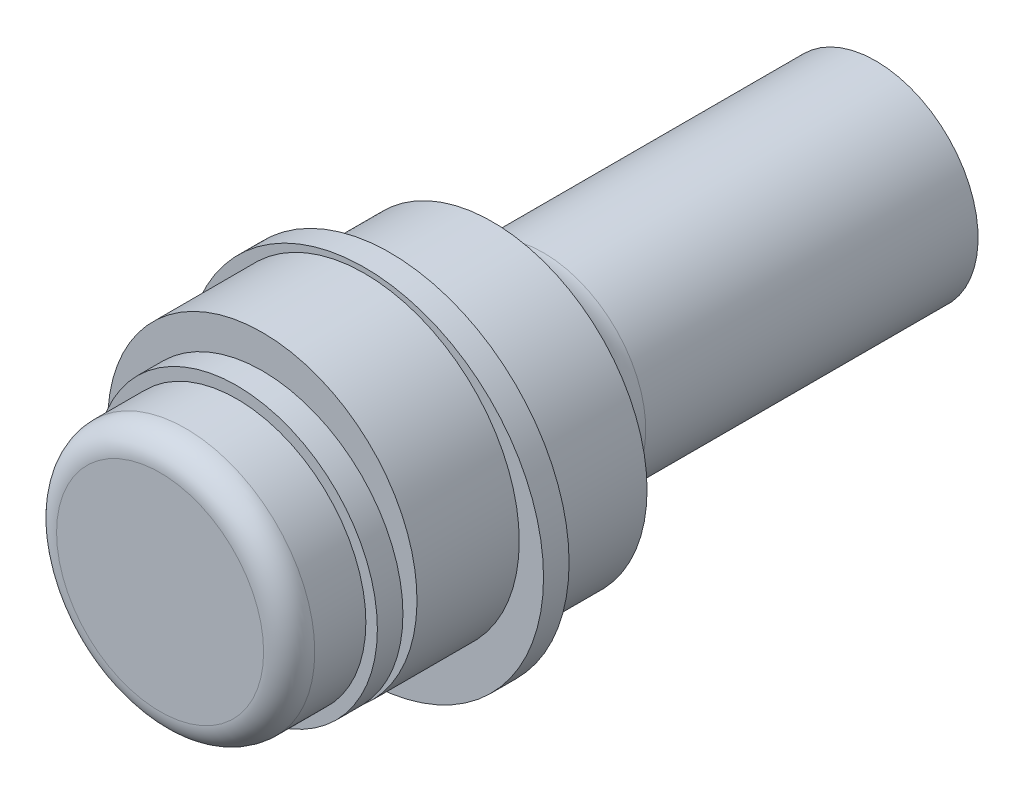
SolidWorks part; units mm, degrees
ref_plane "前视基准面" through (0, 0, 0) normal (0, 0, 1) x (1, 0, 0)
ref_plane "上视基准面" through (0, 0, 0) normal (0, 1, 0) x (1, 0, 0)
ref_plane "右视基准面" through (0, 0, 0) normal (1, 0, 0) x (0, 0, -1)
sketch "草图1" plane through (0, 0, 0) normal (0, 0, 1) x (1, 0, 0)
  circle A0 centre (0, 0) radius 6.05
  dimension "D1" = 12.1
extrude "凸台-拉伸1" add sketch "草图1" along normal blind 5
sketch "草图7" plane through (0, 0, 5) normal (0, 0, 1) x (1, 0, 0)
  circle A0 centre (0, 0) radius 7
  dimension "D1" = 14
extrude "凸台-拉伸6" add sketch "草图7" against normal blind 1
sketch "草图2" plane through (0, 0, 5) normal (0, 0, 1) x (1, 0, 0)
  circle A0 centre (0, 0.75) radius 6.05
  point P0 (0, 0.75)
  dimension "D2" = 12.1
  dimension "D1" = 0.75
extrude "凸台-拉伸2" add sketch "草图2" along normal blind 4
sketch "草图4" plane through (0, 0, 0) normal (0, 0, -1) x (-1, 0, 0)
  line L0 (-2.6458, -3) -> (2.6458, -3)
  circle A0 centre (0, 0) radius 4
  dimension "D1" = 8
  dimension "D2" = 3
extrude "凸台-拉伸3" add sketch "草图4" along normal blind 15 contours L0 A0
fillet "圆角1" radius 2 2 edges at (0, 4, 0) (0, -3, 0)
sketch "草图5" plane through (0, 0, 9) normal (0, 0, 1) x (1, 0, 0)
  circle A0 centre (0, 0) radius 5.5
  dimension "D1" = 11
extrude "凸台-拉伸4" add sketch "草图5" along normal blind 1
sketch "草图6" plane through (0, 0, 10) normal (0, 0, 1) x (1, 0, 0)
  circle A0 centre (0, 0) radius 5.05
  dimension "D1" = 10.1
extrude "凸台-拉伸5" add sketch "草图6" along normal blind 3
fillet "圆角2" radius 1 1 edges at (5.05, 0, 13)
